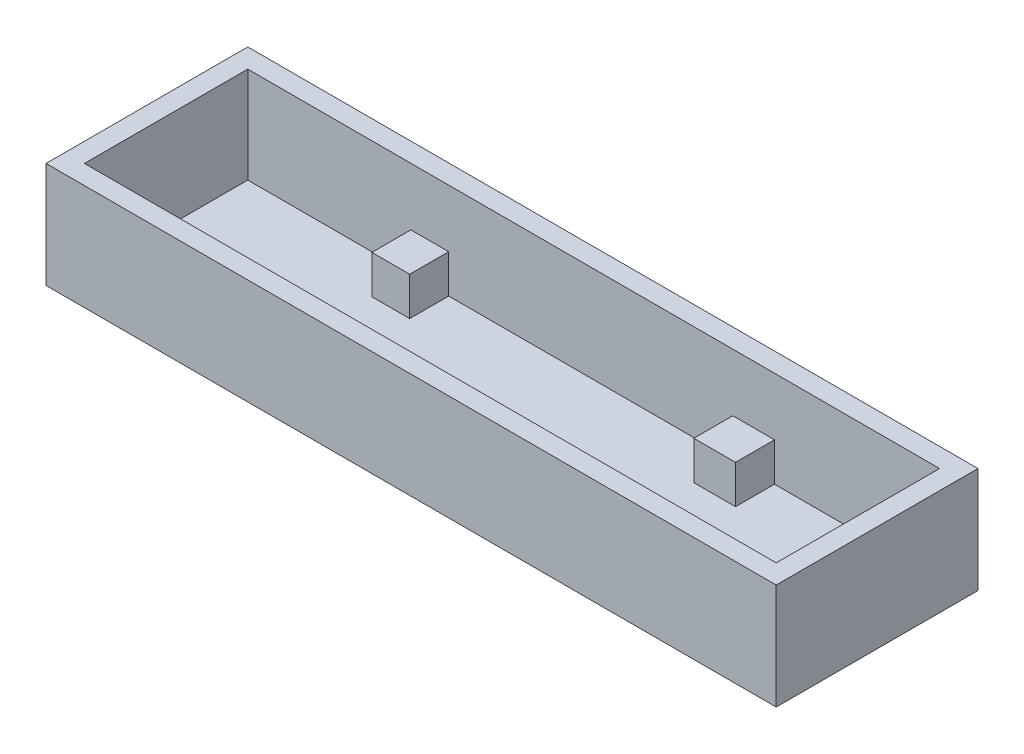
SolidWorks part; units mm, degrees
ref_plane "Front Plane" through (0, 0, 0) normal (0, 0, 1) x (1, 0, 0)
ref_plane "Top Plane" through (0, 0, 0) normal (0, 1, 0) x (1, 0, 0)
ref_plane "Right Plane" through (0, 0, 0) normal (1, 0, 0) x (0, 0, -1)
sketch "Sketch1" plane through (0, 0, 0) normal (0, 1, 0) x (1, 0, 0)
  line L0 (-2, 19) -> (74, 19)
  line L1 (0, 0) -> (72, 0)
  line L2 (0, 0) -> (0, 17)
  line L3 (0, 17) -> (72, 17)
  line L4 (72, 0) -> (72, 17)
  line L5 (74, -2) -> (74, 19)
  line L6 (-2, -2) -> (74, -2)
  line L7 (-2, -2) -> (-2, 19)
  dimension "D1" = 72
  dimension "D2" = 17
  dimension "D3" = 2
extrude "Boss-Extrude1" add sketch "Sketch1" along normal blind 10 contours L7 L6 L5 L0 L4 L1 L2 L3
sketch "Sketch2" plane through (0, 0, 0) normal (0, -1, 0) x (1, 0, 0)
  line L4 (-2, 2) -> (-2, -19)
  line L5 (-2, -19) -> (74, -19)
  line L6 (74, -19) -> (74, 2)
  line L7 (74, 2) -> (-2, 2)
  line L8 (-2, 2) -> (-2, -19)
  line L9 (-2, -19) -> (74, -19)
  line L10 (74, -19) -> (74, 2)
  line L11 (74, 2) -> (-2, 2)
  dimension "D1" = 0
extrude "Boss-Extrude2" add sketch "Sketch2" along normal blind 1
sketch "Sketch3" plane through (0, 0, 0) normal (0, 1, 0) x (1, 0, 0)
  line L0 (0, 17) -> (72, 17) construction
  line L1 (16.975, 17) -> (20.9112, 17)
  line L2 (16.975, 17) -> (16.975, 12.9408)
  line L3 (16.975, 12.9408) -> (20.9112, 12.9408)
  line L4 (20.9112, 17) -> (20.9112, 12.9408)
  line L6 (50.4832, 17) -> (54.8231, 17)
  line L7 (50.4832, 17) -> (50.4832, 12.9408)
  line L8 (50.4832, 12.9408) -> (54.8231, 12.9408)
  line L9 (54.8231, 17) -> (54.8231, 12.9408)
extrude "Boss-Extrude3" add sketch "Sketch3" along normal blind 4
sketch "Sketch4" plane through (0, 0, 0) normal (0, 1, 0) x (1, 0, 0)
  line L0 (0, 0) -> (72, 0) construction
  line L1 (13, 0) -> (18, 0)
  line L2 (13, 0) -> (13, 5)
  line L3 (13, 5) -> (18, 5)
  line L4 (18, 0) -> (18, 5)
  line L5 (0, 0) -> (72, 0) construction
  line L6 (64, 0) -> (59, 0)
  line L7 (64, 0) -> (64, 5)
  line L8 (64, 5) -> (59, 5)
  line L9 (59, 0) -> (59, 5)
  line L10 (0, 0) -> (0, 17) construction
  line L12 (0, 0) -> (0, 17) construction
  dimension "D1" = 5
  dimension "D2" = 13
  dimension "D3" = 5
  dimension "D4" = 59
  dimension "D5" = 5
extrude "Boss-Extrude4" add sketch "Sketch4" along normal blind 4
